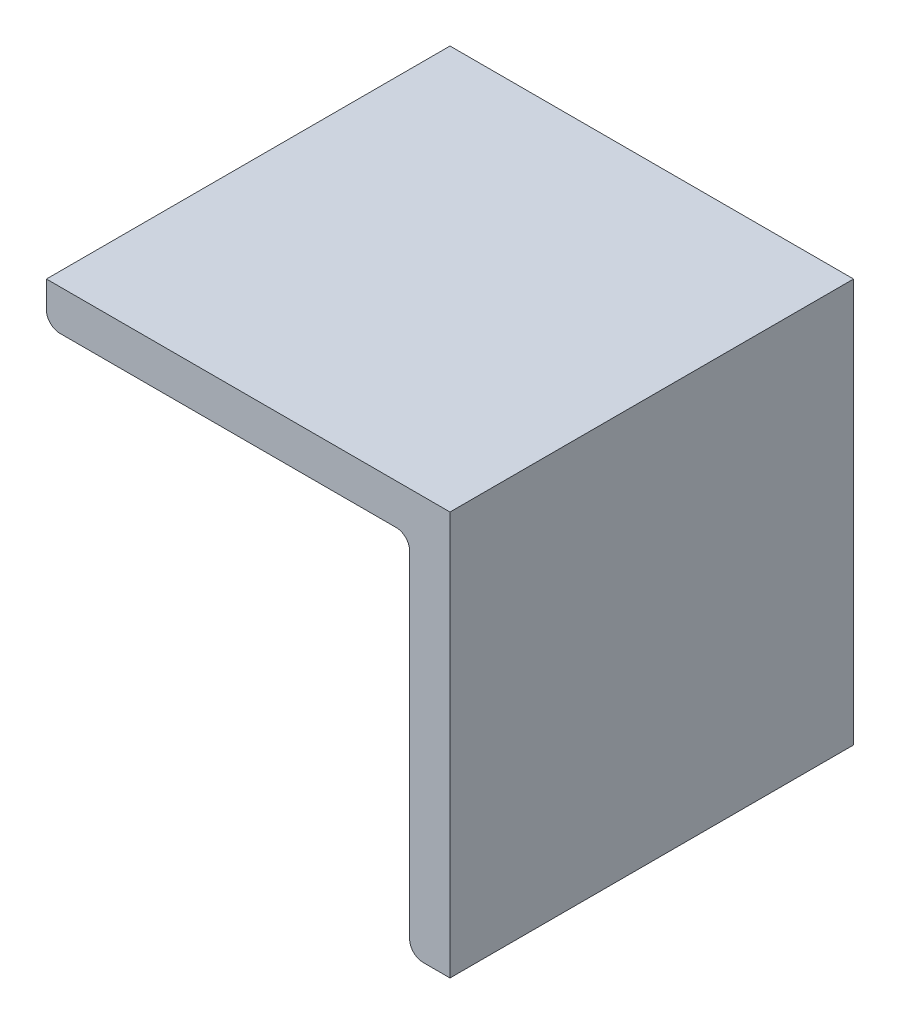
SolidWorks part; units mm, degrees
ref_plane "Alzado" through (0, 0, 0) normal (0, 0, 1) x (1, 0, 0)
ref_plane "Planta" through (0, 0, 0) normal (0, 1, 0) x (1, 0, 0)
ref_plane "Vista lateral" through (0, 0, 0) normal (1, 0, 0) x (0, 0, -1)
sketch "Sketch1" plane through (0, 0, 0) normal (0, 0, 1) x (1, 0, 0)
  line L0 (0, 0) -> (-30, 0)
  line L1 (0, 0) -> (0, -30)
  line L2 (-3, -3) -> (-3, -30)
  line L3 (-3, -3) -> (-30, -3)
  line L4 (0, -30) -> (-3, -30)
  line L5 (-30, 0) -> (-30, -3)
  dimension "D1" = 30
  dimension "D2" = 3
extrude "Extrude1" add sketch "Sketch1" along normal blind 30
fillet "Fillet1" radius 1 3 edges at (-3, -30, 15) (-30, -3, 15) (-3, -3, 15)
